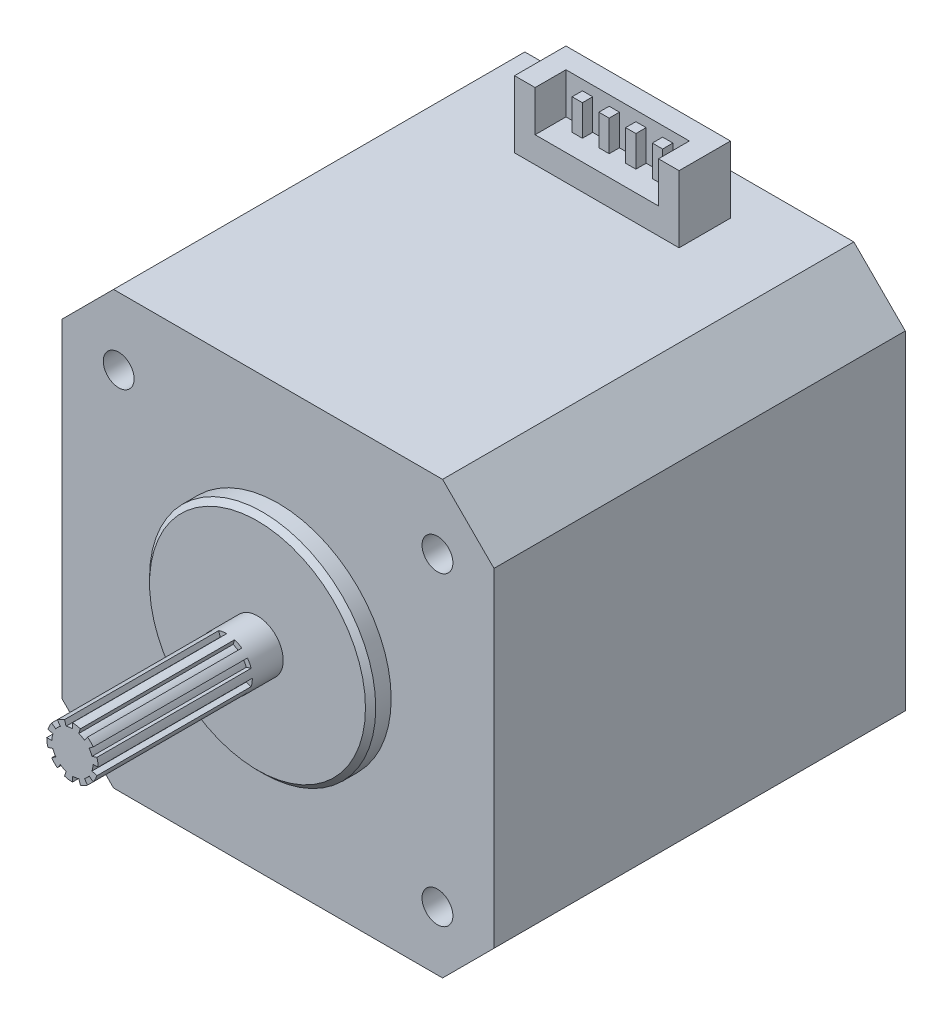
SolidWorks part; units mm, degrees
ref_plane "Ön Düzlem" through (0, 0, 0) normal (0, 0, 1) x (1, 0, 0)
ref_plane "Üst Düzlem" through (0, 0, 0) normal (0, 1, 0) x (1, 0, 0)
ref_plane "Sağ Düzlem" through (0, 0, 0) normal (1, 0, 0) x (0, 0, -1)
sketch "Çizim1" plane through (0, 0, 0) normal (0, 0, 1) x (1, 0, 0)
  line L0 (-21, 16) -> (-16, 21)
  line L1 (-16, 21) -> (16, 21)
  line L2 (-21, 16) -> (-21, -16)
  line L3 (-16, -21) -> (16, -21)
  line L4 (21, 16) -> (21, -16)
  line L5 (-21, 21) -> (21, -21) construction
  line L6 (-21, -21) -> (21, 21) construction
  line L7 (16, 21) -> (21, 16)
  line L8 (-21, -16) -> (-16, -21)
  line L9 (21, -16) -> (16, -21)
  point P0 (0, 0)
  dimension "D1" = 42
  dimension "D2" = 42
extrude "Yükseklik-Ekstrüzyon1" add sketch "Çizim1" along normal blind 40
sketch "Çizim2" plane through (0, 0, 40) normal (0, 0, 1) x (1, 0, 0)
  circle A0 centre (15.5, -15.2593) radius 1.5
  circle A1 centre (-15.5, -15.2593) radius 1.5
  circle A2 centre (-15.5, 14.4626) radius 1.5
  circle A3 centre (15.5, 14.4626) radius 1.5
  point P8 (0, 0)
  point P9 (0, 0)
  point P10 (0, 0)
  point P11 (0, 0)
  dimension "D3" = 3
  dimension "D1" = 31
  dimension "D2" = 15.5
extrude "Kes-Ekstrüzyon1" cut sketch "Çizim2" against normal blind 40
sketch "Çizim3" plane through (0, 0, 40) normal (0, 0, 1) x (1, 0, 0)
  circle A0 centre (0, 0) radius 11
  dimension "D1" = 22
extrude "Yükseklik-Ekstrüzyon2" add sketch "Çizim3" along normal blind 2
chamfer "Pah1" distance 0.5 angle 45 1 edges at (11, 0, 42)
sketch "Çizim4" plane through (0, 0, 42) normal (0, 0, 1) x (1, 0, 0)
  circle A0 centre (0, 0) radius 2.5
  dimension "D1" = 5
extrude "Yükseklik-Ekstrüzyon3" add sketch "Çizim4" along normal blind 18
sketch "Çizim5" plane through (0, 0, 60) normal (0, 0, 1) x (1, 0, 0)
  line L0 (2.5, 0) -> (2, 0)
  line L1 (2.3776, -0.7725) -> (1.9021, -0.618)
  line L2 (2.0225, -1.4695) -> (1.618, -1.1756)
  line L3 (1.4695, -2.0225) -> (1.1756, -1.618)
  line L4 (0.7725, -2.3776) -> (0.618, -1.9021)
  line L5 (0, -2.5) -> (0, -2)
  line L6 (-0.7725, -2.3776) -> (-0.618, -1.9021)
  line L7 (-1.4695, -2.0225) -> (-1.1756, -1.618)
  line L8 (-2.0225, -1.4695) -> (-1.618, -1.1756)
  line L9 (-2.3776, -0.7725) -> (-1.9021, -0.618)
  line L10 (-2.5, 0) -> (-2, 0)
  line L11 (-2.3776, 0.7725) -> (-1.9021, 0.618)
  line L12 (-2.0225, 1.4695) -> (-1.618, 1.1756)
  line L13 (-1.4695, 2.0225) -> (-1.1756, 1.618)
  line L14 (-0.7725, 2.3776) -> (-0.618, 1.9021)
  line L15 (0, 2.5) -> (0, 2)
  line L16 (0.7725, 2.3776) -> (0.618, 1.9021)
  line L17 (1.4695, 2.0225) -> (1.1756, 1.618)
  line L18 (2.0225, 1.4695) -> (1.618, 1.1756)
  line L19 (2.3776, 0.7725) -> (1.9021, 0.618)
  circle A2 centre (0, 0) radius 2.5 construction
  circle A3 centre (0, 0) radius 2.5 construction
  arc A4 (0, -2.5) -> (0.7725, -2.3776) centre (0, 0) ccw
  arc A5 (0, -2) -> (0.618, -1.9021) centre (0, 0) ccw
  circle A6 centre (0, 0) radius 2.5 construction
  circle A7 centre (0, 0) radius 2 construction
  arc A8 (-1.4695, -2.0225) -> (-0.7725, -2.3776) centre (0, 0) ccw
  arc A9 (-1.1756, -1.618) -> (-0.618, -1.9021) centre (0, 0) ccw
  arc A10 (-2.3776, -0.7725) -> (-2.0225, -1.4695) centre (0, 0) ccw
  arc A11 (-1.9021, -0.618) -> (-1.618, -1.1756) centre (0, 0) ccw
  arc A12 (-2.3776, 0.7725) -> (-2.5, 0) centre (0, 0) ccw
  arc A13 (-1.9021, 0.618) -> (-2, 0) centre (0, 0) ccw
  arc A14 (-1.4695, 2.0225) -> (-2.0225, 1.4695) centre (0, 0) ccw
  arc A15 (-1.1756, 1.618) -> (-1.618, 1.1756) centre (0, 0) ccw
  arc A16 (0, 2.5) -> (-0.7725, 2.3776) centre (0, 0) ccw
  arc A17 (0, 2) -> (-0.618, 1.9021) centre (0, 0) ccw
  arc A18 (1.4695, 2.0225) -> (0.7725, 2.3776) centre (0, 0) ccw
  arc A19 (1.1756, 1.618) -> (0.618, 1.9021) centre (0, 0) ccw
  arc A20 (1.9021, 0.618) -> (1.618, 1.1756) centre (0, 0) ccw
  arc A21 (2.3776, 0.7725) -> (2.0225, 1.4695) centre (0, 0) ccw
  arc A22 (1.9021, -0.618) -> (2, 0) centre (0, 0) ccw
  arc A23 (2.3776, -0.7725) -> (2.5, 0) centre (0, 0) ccw
  arc A24 (1.1756, -1.618) -> (1.618, -1.1756) centre (0, 0) ccw
  arc A25 (1.4695, -2.0225) -> (2.0225, -1.4695) centre (0, 0) ccw
  point P49 (0, 0)
  dimension "D2" = 0.5
  dimension "D1" = 20
extrude "Kes-Ekstrüzyon2" cut sketch "Çizim5" against normal blind 15
sketch "Çizim6" plane through (0, 21, 0) normal (0, 1, 0) x (1, 0, 0)
  line L0 (16, 0) -> (-16, 0) construction
  line L1 (8, -9) -> (-8, -9)
  line L2 (8, -9) -> (8, -4)
  line L3 (8, -4) -> (-8, -4)
  line L4 (-8, -9) -> (-8, -4)
  line L5 (8, -9) -> (-8, -4) construction
  line L6 (8, -4) -> (-8, -9) construction
  point P0 (0, -6.5)
  dimension "D1" = 9
  dimension "D2" = 16
  dimension "D3" = 5
extrude "Yükseklik-Ekstrüzyon4" add sketch "Çizim6" along normal blind 6.5
sketch "Çizim7" plane through (0, 0, 9) normal (0, 0, 1) x (1, 0, 0)
  line L0 (6, 27.5) -> (6, 23.526)
  line L1 (6, 23.526) -> (-6, 23.526)
  line L2 (-6, 23.526) -> (-6, 27.5)
  line L4 (-8, 21) -> (8, 21)
  line L5 (8, 21) -> (8, 27.5)
  line L6 (8, 27.5) -> (-8, 27.5)
  line L7 (-8, 27.5) -> (-8, 21)
  line L8 (-8, 21) -> (8, 21)
  line L12 (6, 27.5) -> (-6, 27.5)
  line M11 (8, 27.5) -> (-8, 27.5)
  dimension "D2" = 12
  dimension "D1" = 0
extrude "Kes-Ekstrüzyon3" cut sketch "Çizim7" against normal blind 3 contours L2 L1 L0 M11
sketch "Çizim9" plane through (0, 0, 6) normal (0, 0, 1) x (1, 0, 0)
  line L0 (6, 23.526) -> (-6, 23.526) construction
  line L1 (7, 23.526) -> (6, 23.526)
  line L2 (7, 23.526) -> (7, 26.526)
  line L3 (7, 26.526) -> (6, 26.526)
  line L4 (6, 23.526) -> (6, 26.526)
  line L5 (7, 23.526) -> (6, 26.526) construction
  line L6 (7, 26.526) -> (6, 23.526) construction
  line L7 (6, 27.5) -> (6, 23.526) construction
  line L8 (3.4, 23.526) -> (3.4, 26.526)
  line L9 (4.4, 23.526) -> (4.4, 26.526)
  line L10 (4.4, 26.526) -> (3.4, 26.526)
  line L11 (4.4, 23.526) -> (3.4, 23.526)
  line L12 (0.8, 23.526) -> (0.8, 26.526)
  line L13 (1.8, 23.526) -> (1.8, 26.526)
  line L14 (1.8, 26.526) -> (0.8, 26.526)
  line L15 (1.8, 23.526) -> (0.8, 23.526)
  line L16 (-1.8, 23.526) -> (-1.8, 26.526)
  line L17 (-0.8, 23.526) -> (-0.8, 26.526)
  line L18 (-0.8, 26.526) -> (-1.8, 26.526)
  line L19 (-0.8, 23.526) -> (-1.8, 23.526)
  line L20 (-4.4, 23.526) -> (-4.4, 26.526)
  line L21 (-3.4, 23.526) -> (-3.4, 26.526)
  line L22 (-3.4, 26.526) -> (-4.4, 26.526)
  line L23 (-3.4, 23.526) -> (-4.4, 23.526)
  line L24 (-7, 23.526) -> (-7, 26.526)
  line L25 (-6, 23.526) -> (-6, 26.526)
  line L26 (-6, 26.526) -> (-7, 26.526)
  line L27 (-6, 23.526) -> (-7, 23.526)
  point P9 (-7.25, 25.026)
  line M6 (-6, 23.526) -> (6, 23.526)
  dimension "D1" = 1
  dimension "D2" = 3
  dimension "D3" = 6
extrude "Yükseklik-Ekstrüzyon5" add sketch "Çizim9" along normal blind 1 contours L9 L10 L8 M6 | L13 L14 L12 M6 | L17 L18 L16 M6 | L21 L22 L20 M6
